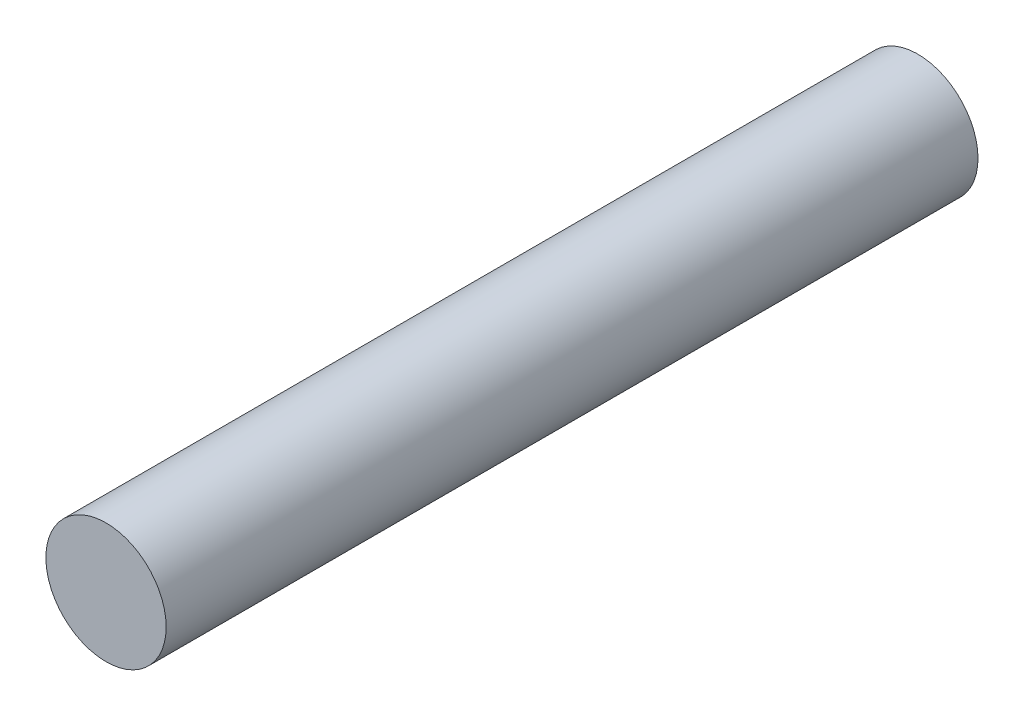
SolidWorks part; units mm, degrees
ref_plane "前视基准面" through (0, 0, 0) normal (0, 0, 1) x (1, 0, 0)
ref_plane "上视基准面" through (0, 0, 0) normal (0, 1, 0) x (1, 0, 0)
ref_plane "右视基准面" through (0, 0, 0) normal (1, 0, 0) x (0, 0, -1)
sketch "草图1" plane through (0, 0, 0) normal (0, 0, 1) x (1, 0, 0)
  circle A0 centre (0, 0) radius 1
extrude "凸台-拉伸1" add sketch "草图1" along normal blind 13.5
